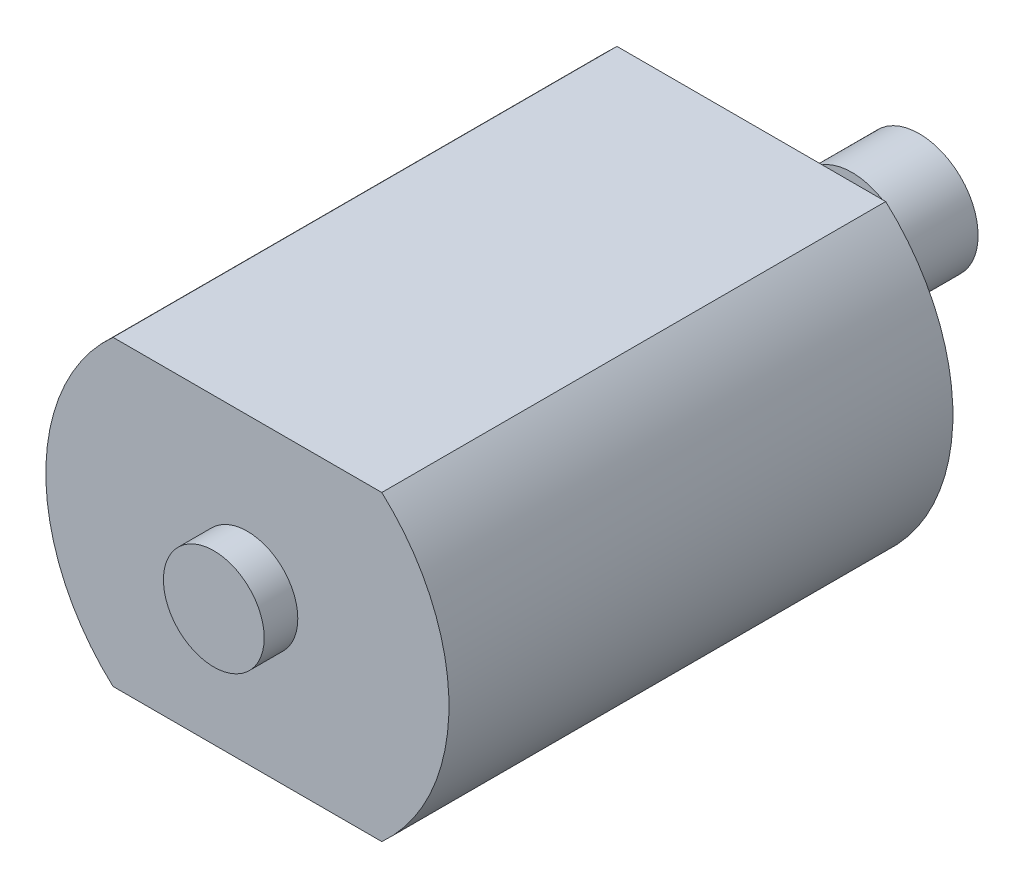
SolidWorks part; units mm, degrees
ref_plane "Front Plane" through (0, 0, 0) normal (0, 0, 1) x (1, 0, 0)
ref_plane "Top Plane" through (0, 0, 0) normal (0, 1, 0) x (1, 0, 0)
ref_plane "Right Plane" through (0, 0, 0) normal (1, 0, 0) x (0, 0, -1)
sketch "Sketch1" plane through (0, 0, 0) normal (0, 1, 0) x (1, 0, 0)
  line L1 (-8, 0) -> (8, 0)
  line L2 (-8, 0) -> (-8, -30)
  line L3 (-8, -30) -> (8, -30)
  line L4 (8, 0) -> (8, -30)
  point P4 (0, 0)
  dimension "D1" = 30
  dimension "D2" = 16
extrude "Boss-Extrude1" add sketch "Sketch1" along normal mid plane 18
sketch "Sketch2" plane through (0, 0, 0) normal (0, 0, -1) x (-1, 0, 0)
  circle A0 centre (0, 0) radius 3
  dimension "D1" = 6
extrude "Boss-Extrude2" add sketch "Sketch2" along normal blind 1
sketch "Sketch3" plane through (0, 0, 30) normal (0, 0, 1) x (1, 0, 0)
  circle A0 centre (0, 0) radius 3
  dimension "D1" = 6
extrude "Boss-Extrude3" add sketch "Sketch3" along normal blind 2
sketch "Sketch5" plane through (0, 0, 0) normal (0, 0, 1) x (1, 0, 0)
  line L0 (8, 9) -> (8, -9) construction
  line L1 (8, 9) -> (8, -9)
  line L2 (-8, 9) -> (-8, -9)
  line L3 (0.125, 0) -> (-0.125, 0) construction
  arc A0 (8, 9) -> (8, -9) centre (-0.125, 0) cw
  arc A1 (-8, 9) -> (-8, -9) centre (0.125, 0) ccw
  point P6 (0, 0)
  dimension "D1" = 24
extrude "Boss-Extrude4" add sketch "Sketch5" along normal up to surface (30 mm away) up to face at (3, 0, 30)
sketch "Sketch6" plane through (0, 0, 0) normal (0, 0, -1) x (-1, 0, 0)
  circle A0 centre (0, 0) radius 0.75
  dimension "D1" = 1.5
extrude "Boss-Extrude5" add sketch "Sketch6" along normal blind 10
sketch "Sketch7" plane through (0, 0, -10) normal (0, 0, -1) x (-1, 0, 0)
  circle A0 centre (0, 0) radius 3.5
  dimension "D1" = 7
extrude "Boss-Extrude6" add sketch "Sketch7" against normal blind 4
